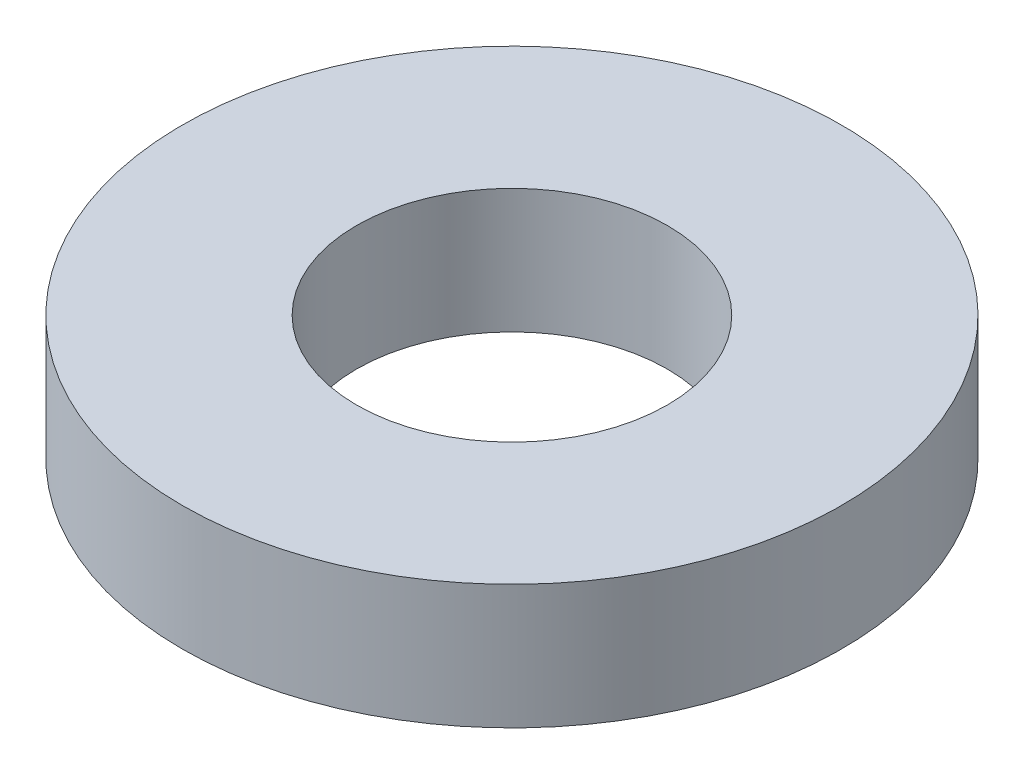
SolidWorks part; units mm, degrees
ref_plane "Front Plane" through (0, 0, 0) normal (0, 0, 1) x (1, 0, 0)
ref_plane "Top Plane" through (0, 0, 0) normal (0, 1, 0) x (1, 0, 0)
ref_plane "Right Plane" through (0, 0, 0) normal (1, 0, 0) x (0, 0, -1)
sketch "Sketch1" plane through (0, 0, 0) normal (0, 1, 0) x (1, 0, 0)
  circle A0 centre (0, 0) radius 1.5875
  circle A1 centre (0, 0) radius 3.3655
  dimension "D1" = 1.778
  dimension "D2" = 3.175
extrude "Boss-Extrude1" add sketch "Sketch1" along normal blind 1.27
equation "\".f\"=1.37937"
